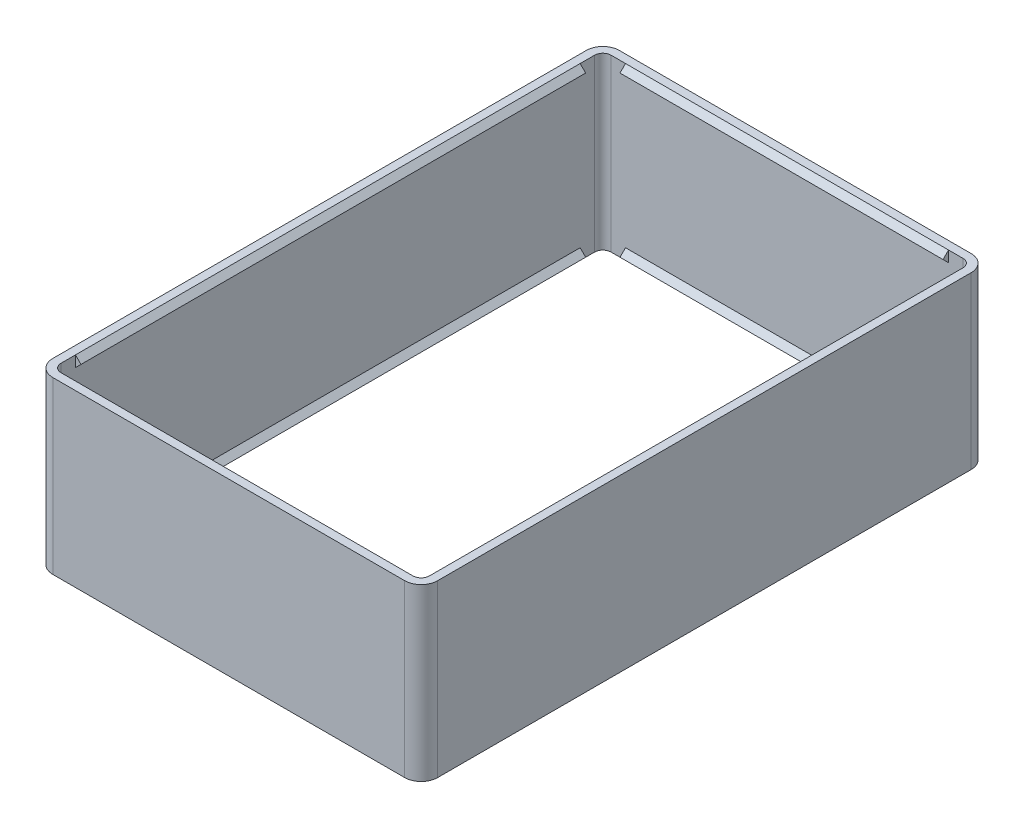
SolidWorks part; units mm, degrees
ref_plane "Front Plane" through (0, 0, 0) normal (0, 0, 1) x (1, 0, 0)
ref_plane "Top Plane" through (0, 0, 0) normal (0, 1, 0) x (1, 0, 0)
ref_plane "Right Plane" through (0, 0, 0) normal (1, 0, 0) x (0, 0, -1)
sketch "Sketch1" plane through (0, 0, 0) normal (0, 1, 0) x (1, 0, 0)
  line L1 (-30.48, -46.99) -> (30.48, -46.99) construction
  line L2 (-30.48, -46.99) -> (-30.48, 46.99) construction
  line L3 (-30.48, 46.99) -> (30.48, 46.99) construction
  line L4 (30.48, -46.99) -> (30.48, 46.99) construction
  line L5 (-30.48, -46.99) -> (30.48, 46.99) construction
  line L6 (-30.48, 46.99) -> (30.48, -46.99) construction
  line L7 (-34.98, -51.49) -> (34.98, -51.49)
  line L8 (-34.98, -51.49) -> (-34.98, 51.49)
  line L9 (-34.98, 51.49) -> (34.98, 51.49)
  line L10 (34.98, -51.49) -> (34.98, 51.49)
  line L11 (-34.98, -51.49) -> (34.98, 51.49) construction
  line L12 (-34.98, 51.49) -> (34.98, -51.49) construction
  line L13 (33.48, -49.99) -> (-33.48, -49.99)
  line L14 (33.48, -49.99) -> (33.48, 49.99)
  line L15 (33.48, 49.99) -> (-33.48, 49.99)
  line L16 (-33.48, -49.99) -> (-33.48, 49.99)
  line L17 (33.48, -49.99) -> (-33.48, 49.99) construction
  line L18 (33.48, 49.99) -> (-33.48, -49.99) construction
  point P0 (0, 0)
  point P6 (0, 0)
  point P11 (0, 0)
  dimension "D1" = 60.96
  dimension "D2" = 93.98
  dimension "D3" = 4.5
  dimension "D4" = 4.5
  dimension "D5" = 1.5
  dimension "D6" = 1.5
extrude "Boss-Extrude1" add sketch "Sketch1" along normal blind 31.0002
fillet "Fillet1" radius 3 4 edges at (-34.98, 15.5001, 51.49) (34.98, 15.5001, 51.49) (34.98, 15.5001, -51.49) (-34.98, 15.5001, -51.49)
fillet "Fillet2" radius 1.5 4 edges at (-33.48, 15.5001, 49.99) (-33.48, 15.5001, -49.99) (33.48, 15.5001, 49.99) (33.48, 15.5001, -49.99)
ref_plane "Plane1" through (-29.3587, 0, 0) normal (1, 0, 0) x (0, 0, -1)
ref_plane "Plane2" through (0, 0, 45.8687) normal (0, 0, -1) x (-1, 0, 0)
ref_plane "Plane3" through (0, 0, -45.8687) normal (0, 0, 1) x (1, 0, 0)
ref_plane "Plane4" through (29.3587, 0, 0) normal (-1, 0, 0) x (0, 0, 1)
sketch "Sketch2" plane through (0, 0, 0) normal (1, 0, 0) x (0, 0, -1)
  line L0 (-49.99, 31.0002) -> (-49.99, 29.0002)
  line L1 (-48.49, 31.0002) -> (-51.49, 31.0002) construction
  line L2 (-49.99, 0) -> (-49.99, 31.0002) construction
  line L3 (-49.99, 29.0002) -> (-48.99, 30.0002)
  line L4 (-48.99, 30.0002) -> (-49.99, 31.0002)
  line L5 (49.99, 31.0002) -> (49.99, 29.0002)
  line L6 (49.99, 31.0002) -> (49.99, 0) construction
  line L7 (49.99, 29.0002) -> (48.99, 30.0002)
  line L8 (48.99, 30.0002) -> (49.99, 31.0002)
  line L9 (-49.99, 0) -> (-49.99, 2)
  line L10 (-51.49, 0) -> (-48.49, 0) construction
  line L11 (-49.99, 2) -> (-48.99, 1)
  line L12 (-48.99, 1) -> (-49.99, 0)
  line L13 (49.99, 0) -> (49.99, 2)
  line L14 (48.49, 0) -> (51.49, 0) construction
  line L15 (49.99, 2) -> (48.99, 1)
  line L16 (48.99, 1) -> (49.99, 0)
  dimension "D1" = 2
  dimension "D2" = 2
  dimension "D3" = 1.4142
  dimension "D4" = 1.4142
  dimension "D5" = 2
  dimension "D6" = 1.4142
  dimension "D7" = 2
  dimension "D8" = 1.4142
extrude "Boss-Extrude2" add sketch "Sketch2" along normal up to surface and the other way up to surface
sketch "Sketch3" plane through (0, 0, 0) normal (0, 0, 1) x (1, 0, 0)
  line L0 (-33.48, 31.0002) -> (-33.48, 29.0002)
  line L1 (-31.98, 31.0002) -> (-34.98, 31.0002) construction
  line L2 (-33.48, 0) -> (-33.48, 31.0002) construction
  line L3 (-33.48, 29.0002) -> (-32.48, 30.0002)
  line L4 (-32.48, 30.0002) -> (-33.48, 31.0002)
  line L5 (-33.48, 0) -> (-33.48, 2)
  line L6 (-33.48, 2) -> (-32.48, 1)
  line L7 (-32.48, 1) -> (-33.48, 0)
  line L8 (33.48, 31.0002) -> (33.48, 29.0002)
  line L9 (33.48, 31.0002) -> (33.48, 0) construction
  line L10 (33.48, 29.0002) -> (32.48, 30.0002)
  line L11 (32.48, 30.0002) -> (33.48, 31.0002)
  line L12 (33.48, 0) -> (33.48, 2)
  line L13 (33.48, 2) -> (32.48, 1)
  line L14 (32.48, 1) -> (33.48, 0)
  dimension "D1" = 2
  dimension "D2" = 1.4142
  dimension "D3" = 2
  dimension "D4" = 1.4142
  dimension "D5" = 2
  dimension "D6" = 1.4142
  dimension "D7" = 2
  dimension "D8" = 1.4142
extrude "Boss-Extrude3" add sketch "Sketch3" against normal up to surface and the other way up to surface
equation "\"D1@Sketch1\"=\"WIDTH\""
equation "\"D2@Sketch1\"= \"LENGTH\""
equation "\"D1@Boss-Extrude1\"=\"TOP_CLEAR\"+\"BOTTOM_CLEAR\"+\"PCB_THICK\""
equation "\"LENGTH\"= 3.7in\t\t\t'longest of two dimensions of pcb"
equation "\"WIDTH\"= 2.4in\t\t\t'shortest of two dimensions of pcb"
equation "\"HOLE_DIA\"= 0.1in\t\t'mounting hole diameter"
equation "\"HOLE_DIST\"= .1375069in\t\t'distance to mount hole centerline from edge of PCB"
equation "\"PCB_THICK\"= 0.063in\t\t'nominal thickness of PCB, usually 1.6mm"
equation "\"TOP_CLEAR\"= 1in\t\t'Clearance above top of PCB, tallest component plus desired clearance"
equation "\"BOTTOM_CLEAR\"= 4mm\t\t'Clearance below bottom of PCB, minimum 4mm"
